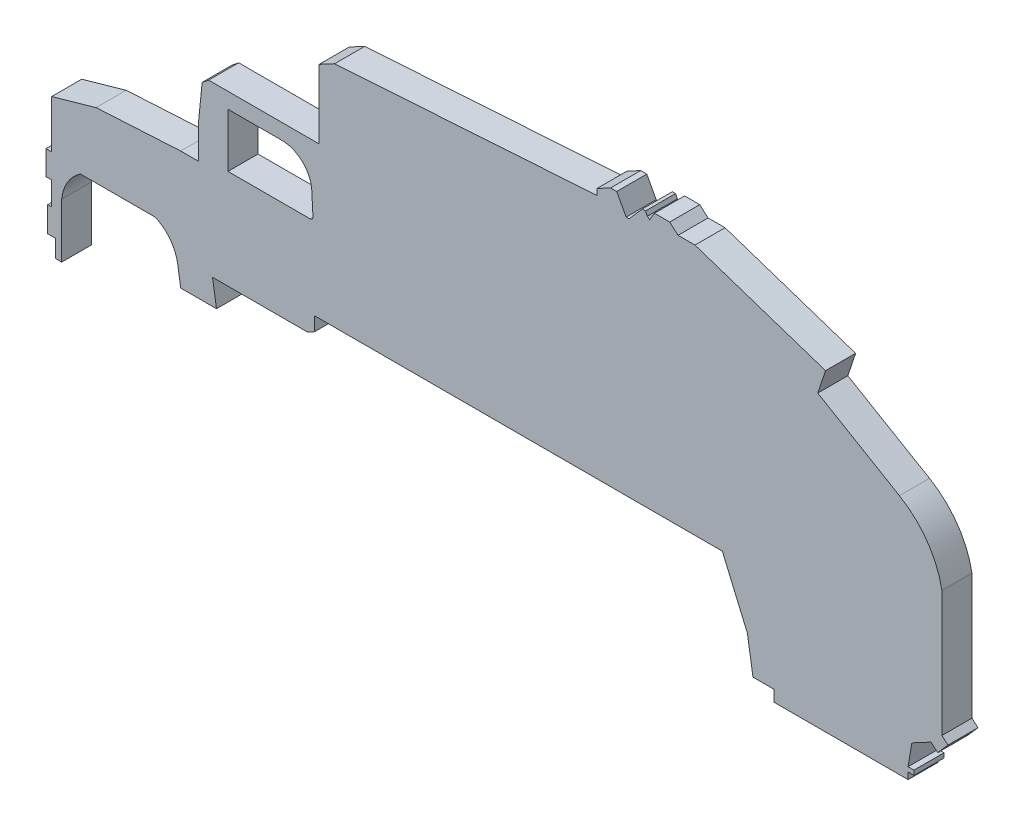
SolidWorks part; units mm, degrees
material "Plain Carbon Steel"
ref_plane "Front Plane" through (0, 0, 0) normal (0, 0, 1) x (1, 0, 0)
ref_plane "Top Plane" through (0, 0, 0) normal (0, 1, 0) x (1, 0, 0)
ref_plane "Right Plane" through (0, 0, 0) normal (1, 0, 0) x (0, 0, -1)
sketch "Sketch1" plane through (0, 0, 0) normal (0, 0, 1) x (1, 0, 0)
  line L0 (14.0723, 26.7793) -> (70.3614, 26.7793) construction
  line L1 (5.3917, 14.2829) -> (5.3917, 15.7652)
  line L2 (5.3917, 15.7652) -> (4.7413, 15.7652)
  line L3 (4.7413, 15.7652) -> (4.7413, 17.898)
  line L4 (4.7413, 17.898) -> (5.0665, 17.898)
  line L5 (5.0665, 17.898) -> (5.0665, 19.8768)
  line L6 (5.0665, 19.8768) -> (4.5955, 19.8768)
  line L7 (4.5955, 19.8768) -> (4.5955, 21.9243)
  line L8 (4.5955, 21.9243) -> (5.0665, 21.9243)
  line L9 (5.0665, 21.9243) -> (5.0665, 25.9706)
  line L10 (5.0665, 25.9706) -> (8.8277, 27.0437)
  line L11 (8.8277, 27.0437) -> (15.9775, 27.4441)
  line L12 (15.9775, 27.4441) -> (17.4978, 27.4441)
  line L13 (17.4978, 27.4441) -> (17.4978, 28.8206)
  line L14 (17.4978, 28.8206) -> (17.4978, 30.4685)
  line L15 (17.4978, 30.4685) -> (17.7835, 33.3672)
  line L16 (17.7835, 33.3672) -> (18.3352, 33.8079)
  line L17 (18.3352, 33.8079) -> (27.6758, 33.8079)
  line L18 (27.6758, 33.8079) -> (27.6758, 37.1852)
  line L19 (27.6758, 37.1852) -> (27.6758, 39.6337)
  line L20 (27.6758, 39.6337) -> (28.9808, 40.3327)
  line L21 (28.9808, 40.3327) -> (51.1418, 41.772)
  line L22 (51.1418, 41.772) -> (51.1418, 42.2843)
  line L23 (51.1418, 42.2843) -> (52.2967, 42.9028)
  line L24 (52.2967, 42.9028) -> (52.8142, 42.9028)
  line L25 (52.8142, 42.9028) -> (53.6072, 41.4225)
  line L26 (53.6072, 41.4225) -> (53.8538, 41.4225)
  line L27 (53.8538, 41.4225) -> (54.9688, 42.6911)
  line L28 (54.9688, 42.6911) -> (55.24, 42.6911)
  line L29 (55.24, 42.6911) -> (55.404, 42.3849)
  line L30 (55.404, 42.3849) -> (55.5983, 42.2141)
  line L31 (55.5983, 42.2141) -> (56.0031, 42.9028)
  line L32 (56.0031, 42.9028) -> (57.289, 42.9028)
  line L33 (57.289, 42.9028) -> (57.9929, 42.2843)
  line L34 (57.9929, 42.2843) -> (59.4258, 42.2843)
  line L35 (59.4258, 42.2843) -> (70.4543, 38.6094)
  line L36 (70.4543, 38.6094) -> (69.7985, 36.641)
  line L37 (69.7985, 36.641) -> (76.6982, 32.5857)
  line L38 (80.2864, 27.4441) -> (80.2864, 21.7768)
  line L39 (80.2864, 21.7768) -> (80.2864, 16.8316)
  line L40 (80.2864, 16.8316) -> (80.7955, 16.3842)
  line L41 (80.7955, 16.3842) -> (79.9266, 15.3956)
  line L42 (79.9266, 15.3956) -> (79.3642, 15.8899)
  line L43 (79.3642, 15.8899) -> (77.7477, 15.0241)
  line L44 (77.7477, 15.0241) -> (77.4295, 13.1214)
  line L45 (77.4295, 13.1214) -> (77.9279, 13.1214)
  line L46 (77.9279, 13.1214) -> (77.9279, 12.7344)
  line L47 (77.9279, 12.7344) -> (77.4295, 12.7344)
  line L48 (77.4295, 12.7344) -> (77.4295, 12.1732)
  line L49 (77.4295, 12.1732) -> (66.0969, 12.1732)
  line L50 (66.0969, 12.1732) -> (66.0969, 13.1214)
  line L51 (66.0969, 13.1214) -> (64.3246, 13.1214)
  line L52 (64.3246, 13.1214) -> (63.852, 16.1017)
  line L53 (63.852, 16.1017) -> (61.7335, 21.0437)
  line L54 (61.7335, 21.0437) -> (27.289, 21.0437)
  line L55 (27.289, 21.0437) -> (27.289, 19.8768)
  line L56 (27.289, 19.8768) -> (26.6782, 19.5497)
  line L57 (26.6782, 19.5497) -> (18.6613, 19.5497)
  line L58 (18.6613, 19.5497) -> (19, 17.4135)
  line L59 (19, 17.4135) -> (15.9775, 17.4135)
  line L60 (15.9775, 17.4135) -> (15.7129, 19.0821)
  line L61 (13.8137, 21.5256) -> (7.5104, 21.5256)
  line L62 (5.3917, 14.2829) -> (5.9193, 14.2829)
  line L63 (5.9193, 14.2829) -> (5.9193, 18.8874)
  line L64 (27.6758, 33.8079) -> (27.289, 21.0437)
  arc A0 (76.6982, 32.5857) -> (80.2864, 27.4441) centre (72.8888, 26.1044) cw
  arc A1 (15.7129, 19.0821) -> (13.8137, 21.5256) centre (12.5453, 18.5798) ccw
  arc A2 (5.9193, 18.8874) -> (7.5104, 21.5256) centre (9.5003, 18.5266) cw
  dimension "D1" = 76.2
  dimension "D2" = 28.62
  dimension "D3" = 34.4445
  dimension "D4" = 80.989
  dimension "D5" = 208.175
  dimension "D6" = 4.942
  dimension "D7" = 113.204
extrude "Boss-Extrude1" add sketch "Sketch1" along normal blind 2.54 contours L17 L18 L19 L20 L21 L22 L23 L24 L25 L26 L27 L28 L29 L30 L31 L32 L33 L34 L35 L36 L37 A0 L38 L39 L40 L41 L42 L43 L44 L45 L46 L47 L48 L49 L50 L51 L52 L53 L54 L55 L56 L57 L58 L59 L60 A1 L61 A2 L63 L62 L1 L2 L3 L4 L5 L6 L7 L8 L9 L10 L11 L12 L13 L14 L15 L16
sketch "Sketch2" plane through (0, 0, 2.54) normal (0, 0, 1) x (1, 0, 0)
  line L12 (19.9674, 32.4965) -> (24.5127, 32.4965)
  line L13 (19.9674, 27.9469) -> (19.9674, 32.4965)
  line L14 (27.1515, 28.2147) -> (27.0489, 30.0949)
  line L15 (19.9674, 27.9469) -> (26.8979, 27.9469)
  arc A0 (27.0489, 30.0949) -> (24.5127, 32.4965) centre (24.5127, 29.9565) ccw
  arc A1 (27.1515, 28.2147) -> (26.8979, 27.9469) centre (26.8979, 28.2009) cw
  point P1 (27.1661, 27.9469)
  point P9 (27.1661, 27.9469)
  dimension "D2" = 2.54
  dimension "D1" = 0.254
extrude "Cut-Extrude1" cut sketch "Sketch2" against normal through all both and the other way through all
